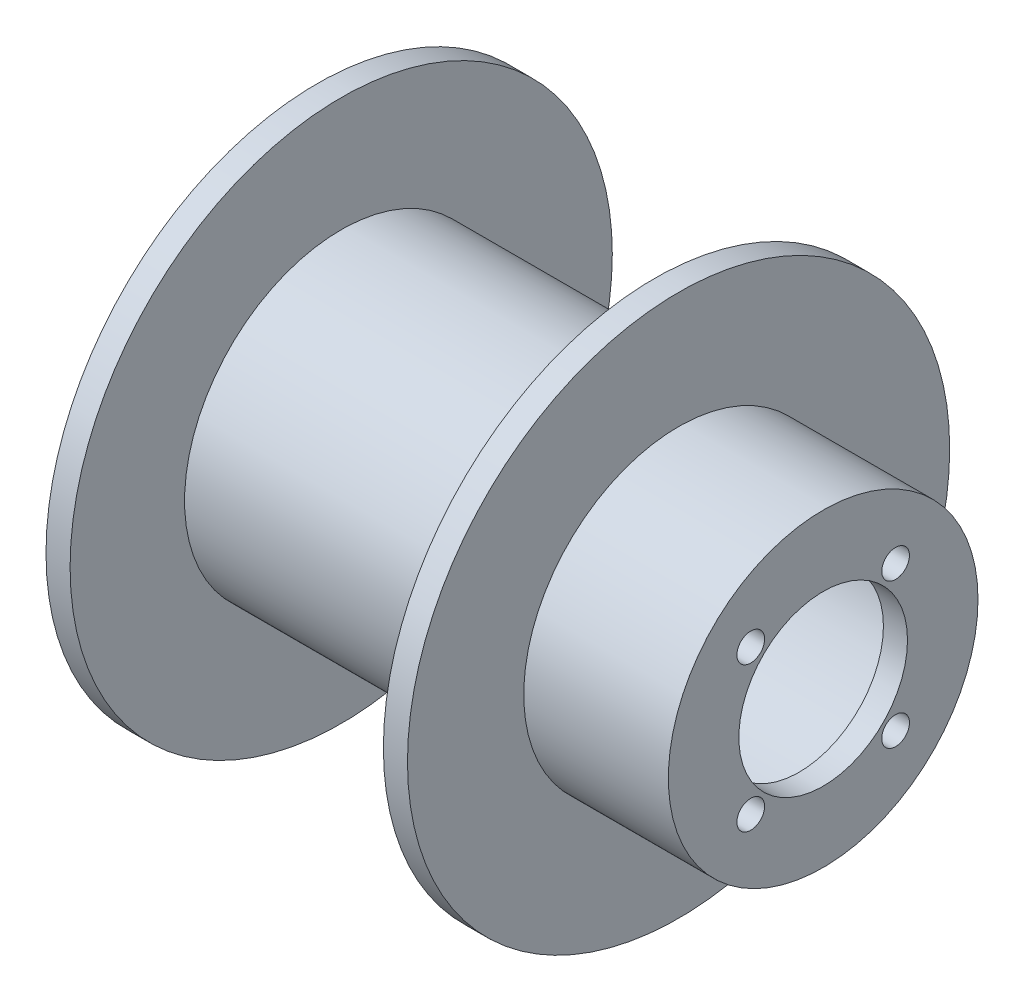
SolidWorks part; units mm, degrees
ref_plane "Front Plane" through (0, 0, 0) normal (0, 0, 1) x (1, 0, 0)
ref_plane "Top Plane" through (0, 0, 0) normal (0, 1, 0) x (1, 0, 0)
ref_plane "Right Plane" through (0, 0, 0) normal (1, 0, 0) x (0, 0, -1)
sketch "Sketch2" plane through (0, 0, 0) normal (1, 0, 0) x (0, 0, -1)
  circle A1 centre (0, 0) radius 12
  circle A2 centre (0, 0) radius 12.85
  dimension "D2" = 24
  dimension "D3" = 25.7
extrude "Boss-Extrude2" add sketch "Sketch2" against normal blind 14 contours A2 A1
sketch "Sketch3" plane through (0, 0, 0) normal (1, 0, 0) x (0, 0, -1)
  circle A0 centre (0, 0) radius 12.85
  circle A1 centre (0, 0) radius 7
  dimension "D1" = 14
  dimension "D2" = 25.7
extrude "Boss-Extrude3" add sketch "Sketch3" against normal blind 2
sketch "Sketch4" plane through (0, 0, 0) normal (1, 0, 0) x (0, 0, -1)
  circle A0 centre (0, 0) radius 22.5
  circle A1 centre (0, 0) radius 12
  dimension "D1" = 45
  dimension "D2" = 24
extrude "Boss-Extrude5" add sketch "Sketch4" along normal blind 2 from surface at -14 starting at face at (-14, 0, -12)
sketch "Sketch6" plane through (0, 0, 0) normal (1, 0, 0) x (0, 0, -1)
  circle A0 centre (0, 0) radius 12
  circle A1 centre (0, 0) radius 13
  dimension "D1" = 24
  dimension "D2" = 26
extrude "Boss-Extrude6" add sketch "Sketch6" against normal blind 26 from surface at -14 starting at face at (-14, 0, -12)
sketch "Sketch7" plane through (0, 0, 0) normal (1, 0, 0) x (0, 0, -1)
  circle A0 centre (0, 0) radius 12
  circle A1 centre (0, 0) radius 22.5
  dimension "D1" = 24
  dimension "D2" = 45
extrude "Boss-Extrude7" add sketch "Sketch7" against normal blind 2 from surface at -40 separate body starting at face at (-40, 0, -12)
sketch "Sketch8" plane through (0, 0, 0) normal (1, 0, 0) x (0, 0, -1)
  line L0 (0, 0) -> (0, 22.5) construction
  line L1 (0, 0) -> (22.5, 0) construction
  line L2 (0, 0) -> (15.9099, 15.9099) construction
  circle A0 centre (0, 0) radius 22.5 construction
  circle A1 centre (0, 0) radius 22.5 construction
  circle A2 centre (0, 0) radius 8.5 construction
  circle A3 centre (6.0104, 6.0104) radius 1.15
  circle A4 centre (6.0104, -6.0104) radius 1.15
  circle A5 centre (-6.0104, -6.0104) radius 1.15
  circle A6 centre (-6.0104, 6.0104) radius 1.15
  point P22 (0, 0)
  dimension "D2" = 17
  dimension "D3" = 2.3
  dimension "D1" = 45
  dimension "D4" = 4
extrude "Cut-Extrude1" cut sketch "Sketch8" against normal through all
